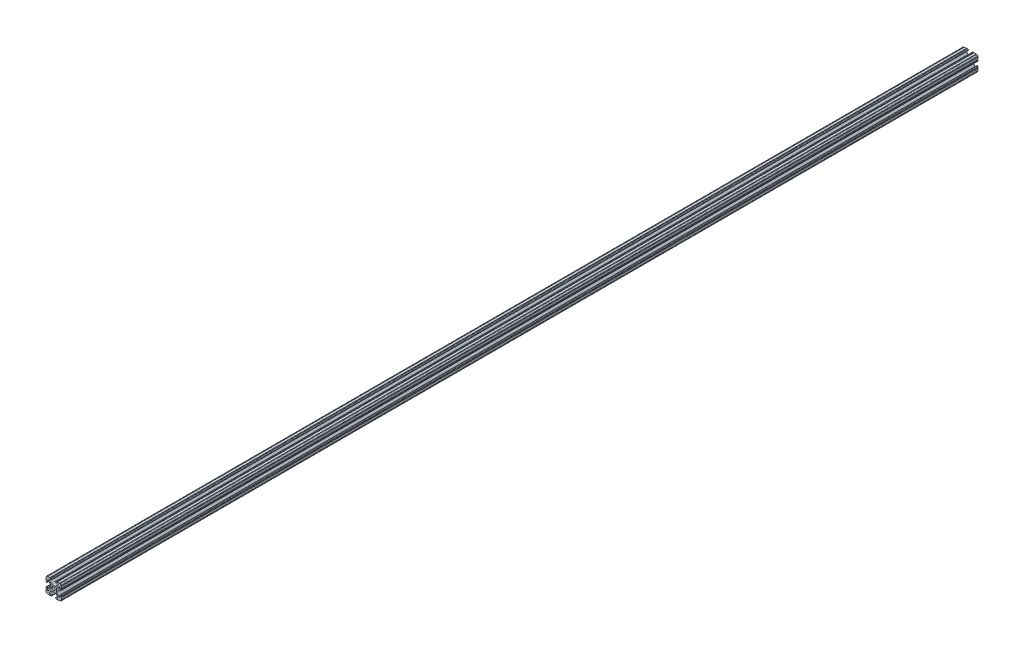
SolidWorks part; units mm, degrees
ref_plane "Front Plane" through (0, 0, 0) normal (0, 0, 1) x (1, 0, 0)
ref_plane "Top Plane" through (0, 0, 0) normal (0, 1, 0) x (1, 0, 0)
ref_plane "Right Plane" through (0, 0, 0) normal (1, 0, 0) x (0, 0, -1)
sketch "Sketch2" plane through (0, 0, 0) normal (0, 0, 1) x (1, 0, 0)
  line L0 (0, 12.7) -> (0, -12.7) construction
  line L1 (-12.7, 0) -> (12.7, 0) construction
  line L2 (3.2512, -12.7) -> (12.7, -12.7)
  line L3 (12.7, -12.7) -> (12.7, -3.2512)
  line L4 (3.2512, -12.7) -> (3.2512, -10.4902)
  line L5 (3.2512, -10.4902) -> (8.9276, -10.4902)
  line L6 (8.9276, -10.4902) -> (3.0856, -4.6482)
  line L7 (0, 0) -> (12.7, -12.7) construction
  line L8 (12.7, -3.2512) -> (10.4902, -3.2512)
  line L9 (10.4902, -3.2512) -> (10.4902, -8.9276)
  line L10 (10.4902, -8.9276) -> (4.6482, -3.0856)
  circle A0 centre (0, 0) radius 2.6035
  arc A1 (6.3485, -10.4902) -> (7.1039, -8.6665) centre (6.3485, -9.4219) ccw construction
  point P8 (0, -4.6482)
  dimension "Center Hole Diameter" = 5.207
  dimension "Rail Height" = 25.4
  dimension "Rail Width" = 25.4
  dimension "T-Slot Width" = 6.5024
  dimension "Slot Inner Width" = 14.8336
  dimension "Thickness" = 2.2098
  dimension "Slot Depth" = 5.842
  dimension "D1" = 2.2098
sketch "Sketch3" plane through (0, 0, 0) normal (1, 0, 0) x (0, 0, -1)
  line L0 (-762, -12.7) -> (762, -12.7) construction
  line L1 (-736.6, 0) -> (736.6, 0) construction
  dimension "Length" = 1524
  dimension "D1" = 25.4
sketch "Sketch4" plane through (0, 0, 0) normal (0, 0, 1) x (1, 0, 0)
  line L0 (4.1904, -12.7) -> (10.1173, -12.7)
  line L1 (3.2512, -12.7) -> (12.7, -12.7) construction
  line L2 (3.2512, -12.7) -> (3.2512, -10.4902) construction
  line L3 (3.2512, -10.4902) -> (8.9276, -10.4902) construction
  line L4 (3.2512, -11.4294) -> (3.2512, -11.7608)
  line L5 (4.1904, -10.4902) -> (6.3485, -10.4902)
  line L6 (0, -4.6482) -> (2.164, -4.6482)
  line L7 (8.9276, -10.4902) -> (3.0856, -4.6482) construction
  line L8 (3.7373, -5.2999) -> (7.1039, -8.6665)
  line L9 (12.7, -12.7) -> (12.7, -3.2512) construction
  line L10 (10.4902, -8.9276) -> (4.6482, -3.0856) construction
  line L11 (10.4902, -3.2512) -> (10.4902, -8.9276) construction
  line L12 (10.4902, -6.3485) -> (10.4902, -4.1904)
  line L13 (12.7, -3.2512) -> (10.4902, -3.2512) construction
  line L14 (11.4294, -3.2512) -> (11.7608, -3.2512)
  line L15 (12.7, -4.1904) -> (12.7, -10.1173)
  line L16 (8.6665, -7.1039) -> (5.2999, -3.7373)
  line L17 (4.6482, 0) -> (4.6482, -2.164)
  line L18 (-12.7, 0) -> (12.7, 0) construction
  line L19 (0, -4.6482) -> (0, -2.6035)
  line L20 (0, 12.7) -> (0, -12.7) construction
  line L21 (4.6482, 0) -> (2.6035, 0)
  arc A0 (3.2512, -11.7608) -> (4.1904, -12.7) centre (4.1904, -11.7608) ccw
  arc A2 (3.2512, -11.4294) -> (4.1904, -10.4902) centre (4.1904, -11.4294) cw
  arc A3 (6.3485, -10.4902) -> (7.1039, -8.6665) centre (6.3485, -9.4219) ccw
  arc A4 (2.164, -4.6482) -> (3.7373, -5.2999) centre (2.164, -6.8732) cw
  arc A5 (10.1173, -12.7) -> (12.7, -10.1173) centre (10.1173, -10.1173) ccw
  arc A6 (8.6665, -7.1039) -> (10.4902, -6.3485) centre (9.4219, -6.3485) ccw
  arc A7 (10.4902, -4.1904) -> (11.4294, -3.2512) centre (11.4294, -4.1904) cw
  arc A8 (11.7608, -3.2512) -> (12.7, -4.1904) centre (11.7608, -4.1904) cw
  arc A9 (5.2999, -3.7373) -> (4.6482, -2.164) centre (6.8732, -2.164) cw
  circle A10 centre (0, 0) radius 2.6035 construction
  arc A11 (0, -2.6035) -> (2.6035, 0) centre (0, 0) ccw
  dimension "D1" = 2.5827
  dimension "D2" = 2.225
  dimension "D3" = 0.9392
extrude "Boss-Extrude1" add sketch "Sketch4" along normal mid plane 1524
sketch "Sketch5" plane through (0, 0, 0) normal (0, 0, 1) x (1, 0, 0)
  line L0 (3.2512, -12.7) -> (12.7, -12.7) construction
  line L1 (4.1904, -10.4902) -> (6.3485, -10.4902) construction
  line L3 (0, 0) -> (12.7, -12.7) construction
  line L4 (6.3485, -10.4902) -> (6.3485, -12.7) construction
  line L5 (8.9276, -10.4902) -> (3.0856, -4.6482) construction
  circle A0 centre (10.3562, -12.7) radius 0.5524
  circle A1 centre (5.796, -12.7) radius 0.5524
  circle A2 centre (12.7, -10.3562) radius 0.5524
  circle A3 centre (12.7, -5.796) radius 0.5524
  point P10 (5.2694, -10.4902)
  point P12 (9.4219, -6.3485)
  dimension "D1" = 1.1049
extrude "Cut-Extrude1" cut sketch "Sketch5" against normal through all both and the other way through all
mirror "Mirror1" about plane through (0, 0, 0) normal (1, 0, 0) of bodies 137 134
mirror "Mirror2" about plane through (0, 0, 0) normal (0, 1, 0) of bodies 135
equation "\"D1@Boss-Extrude1\"=\"Length@Sketch3\""
equation "\"D1@Sketch2\"=\"Thickness@Sketch2\""
equation "\"D2@Sketch4\"=\"Slot Inner Width@Sketch2\"*0.15"
equation "\"D1@Sketch4\"=\"D3@Sketch4\"*2.75"
equation "\"D3@Sketch4\"=\"Thickness@Sketch2\"*0.425"
equation "\"D1@Sketch5\"=\"Thickness@Sketch2\"*0.5"
